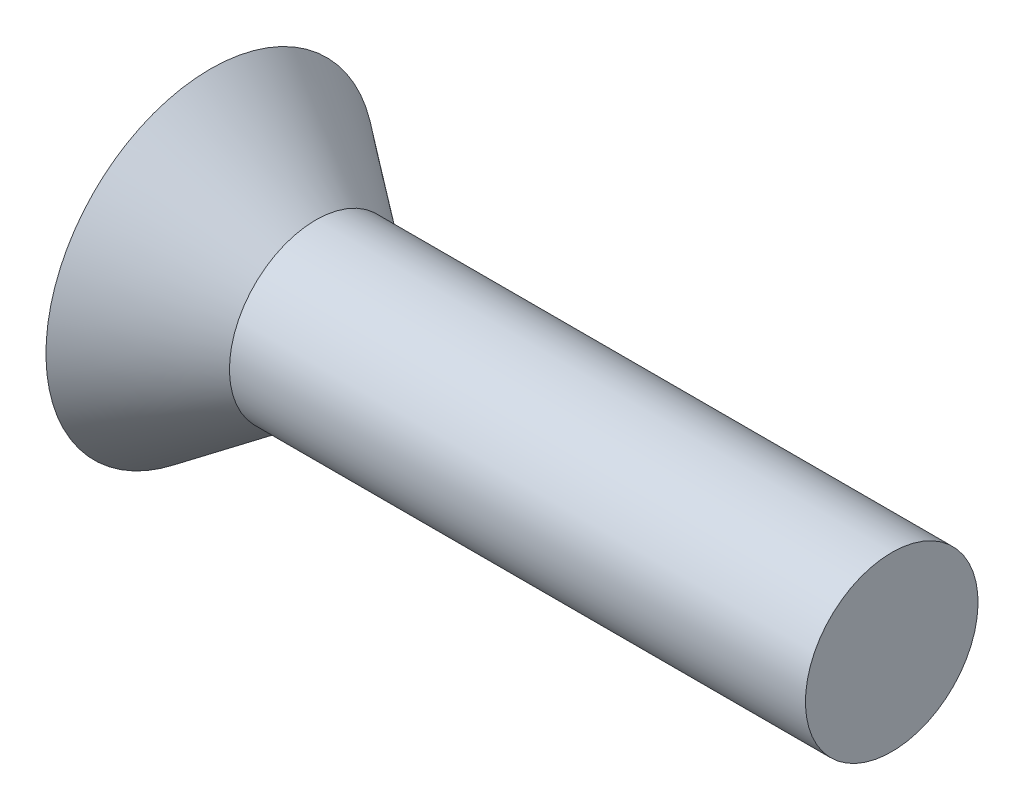
SolidWorks part; units mm, degrees
ref_plane "Front Plane" through (0, 0, 0) normal (0, 0, 1) x (1, 0, 0)
ref_plane "Top Plane" through (0, 0, 0) normal (0, 1, 0) x (1, 0, 0)
ref_plane "Right Plane" through (0, 0, 0) normal (1, 0, 0) x (0, 0, -1)
sketch "Sketch1" plane through (0, 0, 0) normal (0, 0, 1) x (1, 0, 0)
  line L0 (0, 0) -> (16.1036, 0)
  line L5 (-2.9464, -2.1844) -> (0, 0)
  line L6 (22.1649, 2.413) -> (-9.2004, 2.413) construction
  line L7 (-2.9464, -2.1844) -> (-2.9464, 2.413)
  line L8 (16.1036, 0) -> (16.1036, 2.413)
  line L9 (16.1036, 2.413) -> (-2.9464, 2.413)
  dimension "D1" = 19.05
  dimension "D2" = 4.826
  dimension "D3" = 9.1948
  dimension "D4" = 2.9464
revolve "Revolve1" add sketch "Sketch1" angle 360 about L6
